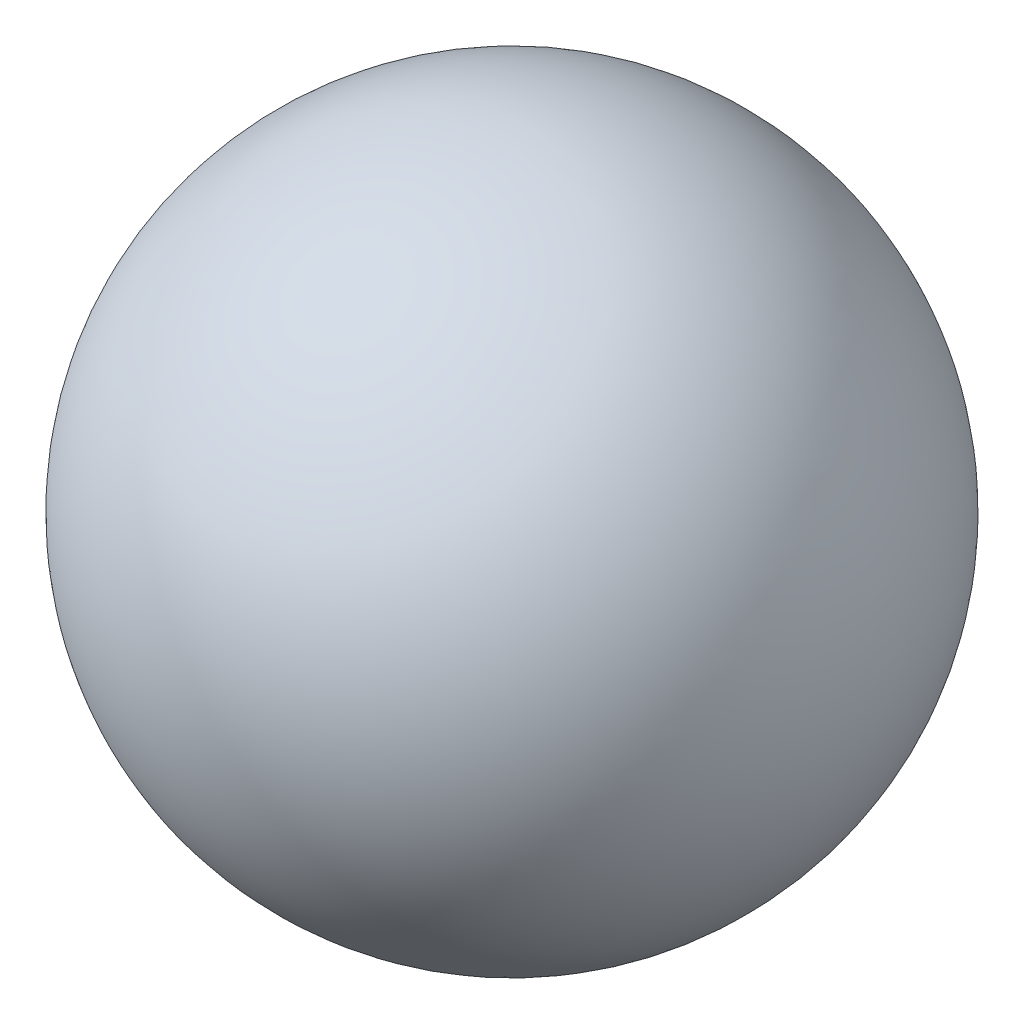
SolidWorks part; units mm, degrees
ref_plane "Front Plane" through (0, 0, 0) normal (0, 0, 1) x (1, 0, 0)
ref_plane "Top Plane" through (0, 0, 0) normal (0, 1, 0) x (1, 0, 0)
ref_plane "Right Plane" through (0, 0, 0) normal (1, 0, 0) x (0, 0, -1)
sketch "Sketch2" plane through (0, 0, 0) normal (0, 1, 0) x (1, 0, 0)
  line L0 (0, 1.5) -> (0, -1.5)
  arc A0 (0, -1.5) -> (0, 1.5) centre (0, 0) cw
  dimension "D1" = 3
revolve "Revolve3" add sketch "Sketch2" angle 360 about L0
